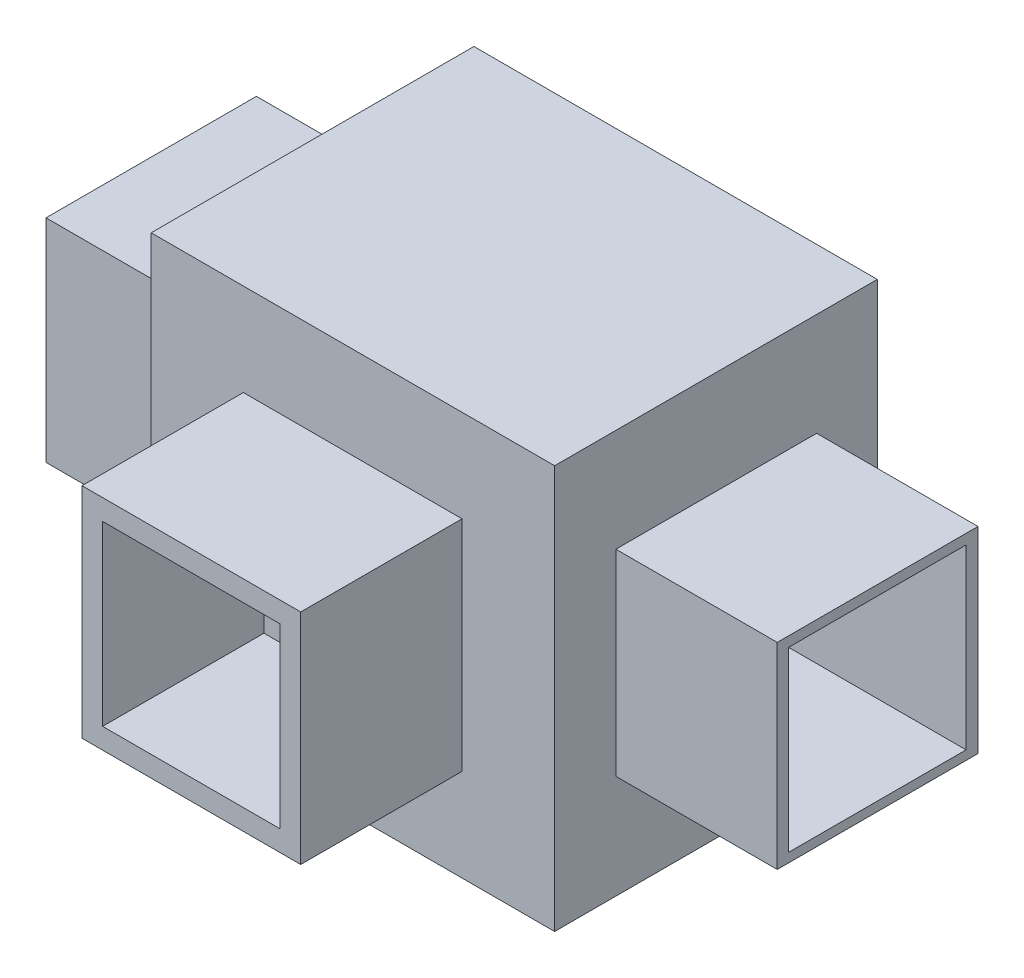
SolidWorks part; units mm, degrees
ref_plane "Alzado" through (0, 0, 0) normal (0, 0, 1) x (1, 0, 0)
ref_plane "Planta" through (0, 0, 0) normal (0, 1, 0) x (1, 0, 0)
ref_plane "Vista lateral" through (0, 0, 0) normal (1, 0, 0) x (0, 0, -1)
sketch "Croquis4" plane through (0, 0, 0) normal (0, 0, 1) x (1, 0, 0)
  line L1 (-81.2466, 21.3933) -> (-31.2466, 21.3933)
  line L2 (-81.2466, 21.3933) -> (-81.2466, -28.6067)
  line L3 (-81.2466, -28.6067) -> (-31.2466, -28.6067)
  line L4 (-31.2466, 21.3933) -> (-31.2466, -28.6067)
extrude "Saliente-Extruir3" add sketch "Croquis4" along normal blind 20
sketch "Croquis5" plane through (0, 0, 20) normal (0, 0, 1) x (1, 0, 0)
  line L3 (-69.8249, 9.9604) -> (-42.7146, 9.9604)
  line L5 (-69.8249, 9.9604) -> (-69.8249, -17.1498)
  line L6 (-67.2698, 7.4053) -> (-45.2698, 7.4053)
  line L7 (-67.2698, 7.4053) -> (-67.2698, -14.5947)
  line L8 (-67.2698, -14.5947) -> (-45.2698, -14.5947)
  line L9 (-45.2698, 7.4053) -> (-45.2698, -14.5947)
  line L10 (-67.2698, 7.4053) -> (-45.2698, -14.5947) construction
  line L11 (-67.2698, -14.5947) -> (-45.2698, 7.4053) construction
  line L12 (-69.8249, -17.1498) -> (-42.7146, -17.1498)
  line L13 (-42.7146, 9.9604) -> (-42.7146, -17.1498)
  line L14 (-69.8249, 9.9604) -> (-42.7146, -17.1498) construction
  line L15 (-69.8249, -17.1498) -> (-42.7146, 9.9604) construction
  point P0 (-56.2698, -3.5947)
  point P5 (-56.2698, -3.5947)
extrude "Saliente-Extruir4" add sketch "Croquis5" along normal blind 20
sketch "Croquis6" plane through (0, 0, 0) normal (0, 0, -1) x (-1, 0, 0)
  line L1 (31.2466, 21.3933) -> (81.2466, 21.3933)
  line L2 (31.2466, 21.3933) -> (31.2466, -28.6067)
  line L3 (31.2466, -28.6067) -> (81.2466, -28.6067)
  line L4 (81.2466, 21.3933) -> (81.2466, -28.6067)
extrude "Saliente-Extruir5" add sketch "Croquis6" along normal blind 20
sketch "Croquis8" plane through (-81.2466, 0, 0) normal (-1, 0, 0) x (0, 0, 1)
  line L4 (-11, 7.3933) -> (11, 7.3933)
  line L5 (-11, 7.3933) -> (-11, -14.6067)
  line L6 (-11, -14.6067) -> (11, -14.6067)
  line L7 (11, 7.3933) -> (11, -14.6067)
  line L8 (-11, 7.3933) -> (11, -14.6067) construction
  line L9 (-11, -14.6067) -> (11, 7.3933) construction
  line L10 (-13.0391, 9.5231) -> (13.0391, 9.5231)
  line L11 (-13.0391, 9.5231) -> (-13.0391, -16.7366)
  line L12 (-13.0391, -16.7366) -> (13.0391, -16.7366)
  line L13 (13.0391, 9.5231) -> (13.0391, -16.7366)
  line L14 (-13.0391, 9.5231) -> (13.0391, -16.7366) construction
  line L15 (-13.0391, -16.7366) -> (13.0391, 9.5231) construction
  point P4 (0, -3.6067)
  point P13 (0, -3.6067)
extrude "Saliente-Extruir6" add sketch "Croquis8" along normal blind 20
sketch "Croquis9" plane through (-81.2466, 0, 0) normal (-1, 0, 0) x (0, 0, 1)
  line L1 (-11, 7.3933) -> (11, 7.3933)
  line L2 (-11, 7.3933) -> (-11, -14.6067)
  line L3 (-11, -14.6067) -> (11, -14.6067)
  line L4 (11, 7.3933) -> (11, -14.6067)
extrude "Cortar-Extruir1" cut sketch "Croquis9" against normal blind 100
sketch "Croquis10" plane through (-31.2466, 0, 0) normal (1, 0, 0) x (0, 0, -1)
  line L1 (-11, 7.3933) -> (11, 7.3933)
  line L2 (-11, 7.3933) -> (-11, -14.6067)
  line L3 (-11, -14.6067) -> (11, -14.6067)
  line L4 (11, 7.3933) -> (11, -14.6067)
  line L5 (-12.4058, 8.6332) -> (12.4786, 8.6332)
  line L6 (-12.4058, 8.6332) -> (-12.4058, -15.7457)
  line L7 (-12.4058, -15.7457) -> (12.4786, -15.7457)
  line L8 (12.4786, 8.6332) -> (12.4786, -15.7457)
extrude "Saliente-Extruir7" add sketch "Croquis10" along normal blind 20
